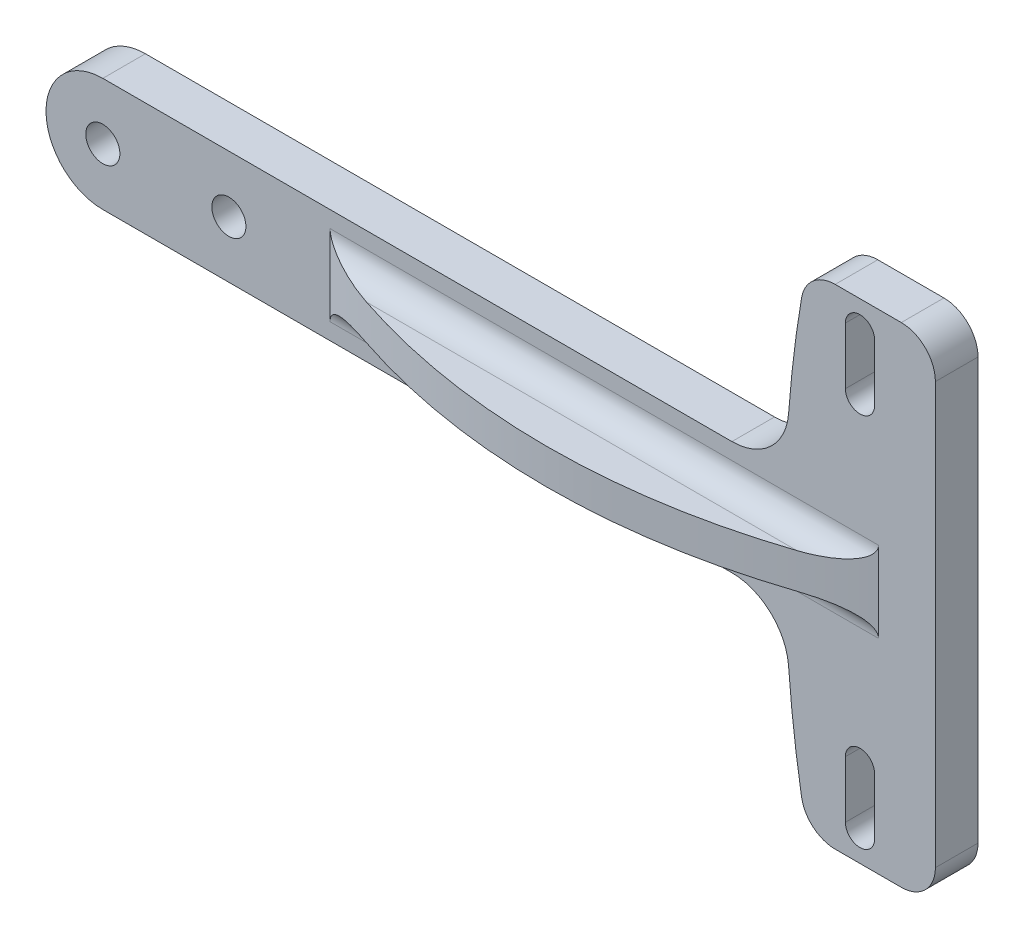
SolidWorks part; units mm, degrees
ref_plane "Front Plane" through (0, 0, 0) normal (0, 0, 1) x (1, 0, 0)
ref_plane "Top Plane" through (0, 0, 0) normal (0, 1, 0) x (1, 0, 0)
ref_plane "Right Plane" through (0, 0, 0) normal (1, 0, 0) x (0, 0, -1)
sketch "Sketch1" plane through (0, 0, 0) normal (0, 0, 1) x (1, 0, 0)
  line L0 (-63.6566, -27.3354) -> (-71.0455, -27.3354) construction
  line L1 (-59.8466, 0) -> (-59.8466, -23.5254) construction
  line L2 (-59.8466, 23.5254) -> (-59.8466, 0) construction
  line L3 (-71.0455, 27.3354) -> (-63.6566, 27.3354) construction
  line L4 (-71.0455, 27.3354) -> (-63.6566, 27.3354)
  line L5 (-59.8466, 23.5254) -> (-59.8466, 0)
  line L6 (-59.8466, 0) -> (-59.8466, -23.5254)
  line L7 (-63.6566, -27.3354) -> (-71.0455, -27.3354)
  line L8 (-68.2739, -24.1604) -> (-68.2739, -17.8104) construction
  line L9 (-69.9059, -24.1604) -> (-69.9059, -17.8104)
  line L10 (-66.642, -24.1604) -> (-66.642, -17.8104)
  line L11 (-74.0409, 0) -> (-59.8466, 0) construction
  line L12 (-68.2739, 24.1604) -> (-68.2739, 17.8104) construction
  line L13 (-69.9059, 24.1604) -> (-69.9059, 17.8104)
  line L14 (-66.642, 24.1604) -> (-66.642, 17.8104)
  line L15 (-82.5872, 6.35) -> (-152.9012, 6.35)
  line L16 (-82.5872, -6.35) -> (-152.9012, -6.35)
  line L17 (-76.7012, 0) -> (-152.9012, 0) construction
  arc A0 (-74.8001, -24.1732) -> (-71.0455, -27.3354) centre (-71.0455, -23.5254) ccw construction
  arc A1 (-63.6566, -27.3354) -> (-59.8466, -23.5254) centre (-63.6566, -23.5254) ccw construction
  arc A2 (-59.8466, 23.5254) -> (-63.6566, 27.3354) centre (-63.6566, 23.5254) ccw construction
  arc A3 (-71.0455, 27.3354) -> (-74.8001, 24.1732) centre (-71.0455, 23.5254) ccw construction
  arc A4 (-71.0455, 27.3354) -> (-74.8001, 24.1732) centre (-71.0455, 23.5254) ccw
  arc A5 (-59.8466, 23.5254) -> (-63.6566, 27.3354) centre (-63.6566, 23.5254) ccw
  arc A6 (-63.6566, -27.3354) -> (-59.8466, -23.5254) centre (-63.6566, -23.5254) ccw
  arc A7 (-74.8001, -24.1732) -> (-71.0455, -27.3354) centre (-71.0455, -23.5254) ccw
  arc A8 (-69.9059, -24.1604) -> (-66.642, -24.1604) centre (-68.2739, -24.1604) ccw
  arc A9 (-66.642, -17.8104) -> (-69.9059, -17.8104) centre (-68.2739, -17.8104) ccw
  arc A10 (-82.5872, 6.35) -> (-76.2554, 12.2198) centre (-82.5872, 12.7) ccw
  arc A11 (-66.642, -17.8104) -> (-69.9059, -17.8104) centre (-68.2739, -17.8104) ccw construction
  arc A12 (-69.9059, 24.1604) -> (-66.642, 24.1604) centre (-68.2739, 24.1604) cw
  arc A13 (-66.642, 17.8104) -> (-69.9059, 17.8104) centre (-68.2739, 17.8104) cw
  arc A14 (-152.9012, 6.35) -> (-152.9012, -6.35) centre (-152.9012, 0) ccw
  arc A15 (-82.5872, -6.35) -> (-76.2554, -12.2198) centre (-82.5872, -12.7) cw
  circle A16 centre (-152.9012, 0) radius 1.905
  circle A17 centre (-138.8118, 0) radius 1.905
  circle A18 centre (-124.7224, 0) radius 1.905
  circle A19 centre (-110.6331, 0) radius 1.905
  circle A20 centre (-96.5437, 0) radius 1.905
  circle A21 centre (-82.4543, 0) radius 1.905
  spline S0 degree 3 poles (-1519.6569, -3729.4535) (1736.5939, 4120.9501) (-2244.6425, -3885.3086) (2430.679, 3060.3502) knots -5.029548 -5.029548 -5.029548 -5.029548 4.927053 4.927053 4.927053 4.927053 only from (-76.7012, 0) to (-36.6507, -70.4667) construction
  spline S1 degree 3 poles (2430.7404, -3060.4414) (-2244.7032, 3885.417) (1736.6521, -4121.0728) (-1519.7108, 3729.5834) knots -3.927097 -3.927097 -3.927097 -3.927097 6.029603 6.029603 6.029603 6.029603 only from (-36.6507, 70.4667) to (-76.7012, 0) construction
  spline S2 degree 3 poles (-74.8001, 24.1732) (-75.4766, 20.2522) (-75.9501, 16.2453) (-76.2554, 12.2198) knots 0.740048 0.740048 0.740048 0.740048 0.869192 0.869192 0.869192 0.869192
  spline S3 degree 3 poles (-76.2554, -12.2198) (-75.9501, -16.2453) (-75.4766, -20.2522) (-74.8001, -24.1732) knots 0.130808 0.130808 0.130808 0.130808 0.259952 0.259952 0.259952 0.259952
  point P5 (-68.2739, -20.9854)
  point P29 (-68.2739, 20.9854)
  dimension "D3" = 6.35
  dimension "D4" = 3.81
  dimension "D1" = 76.2
  dimension "D2" = 6.35
  dimension "D6" = 14.0894
  dimension "D5" = 6
extrude "Boss-Extrude1" add sketch "Sketch1" along normal blind 4.7625
sketch "Sketch2" plane through (0, 0, 0) normal (0, 1, 0) x (1, 0, 0)
  line L0 (-66.1966, -4.7625) -> (-127.5012, -4.7625)
  line L1 (-82.5872, -4.7625) -> (-152.9012, -4.7625) construction
  line L3 (-82.5872, -4.7625) -> (-152.9012, -4.7625) construction
  line L4 (-152.9012, -4.7625) -> (-152.9012, 0) construction
  line L5 (-82.5872, -4.7625) -> (-82.5872, 0) construction
  arc A0 (-66.1966, -4.7625) -> (-127.5012, -4.7625) centre (-96.8489, 65.0005) cw
  point P7 (-63.1891, -3.175)
  dimension "D2" = 76.2
  dimension "D1" = 25.4
  dimension "D3" = 6.35
extrude "Boss-Extrude2" add sketch "Sketch2" along normal mid plane 3.937
fillet "Fillet1" radius 2.54 2 edges at (-96.8489, -1.9685, 4.7625) (-96.8489, 1.9685, 4.7625)
